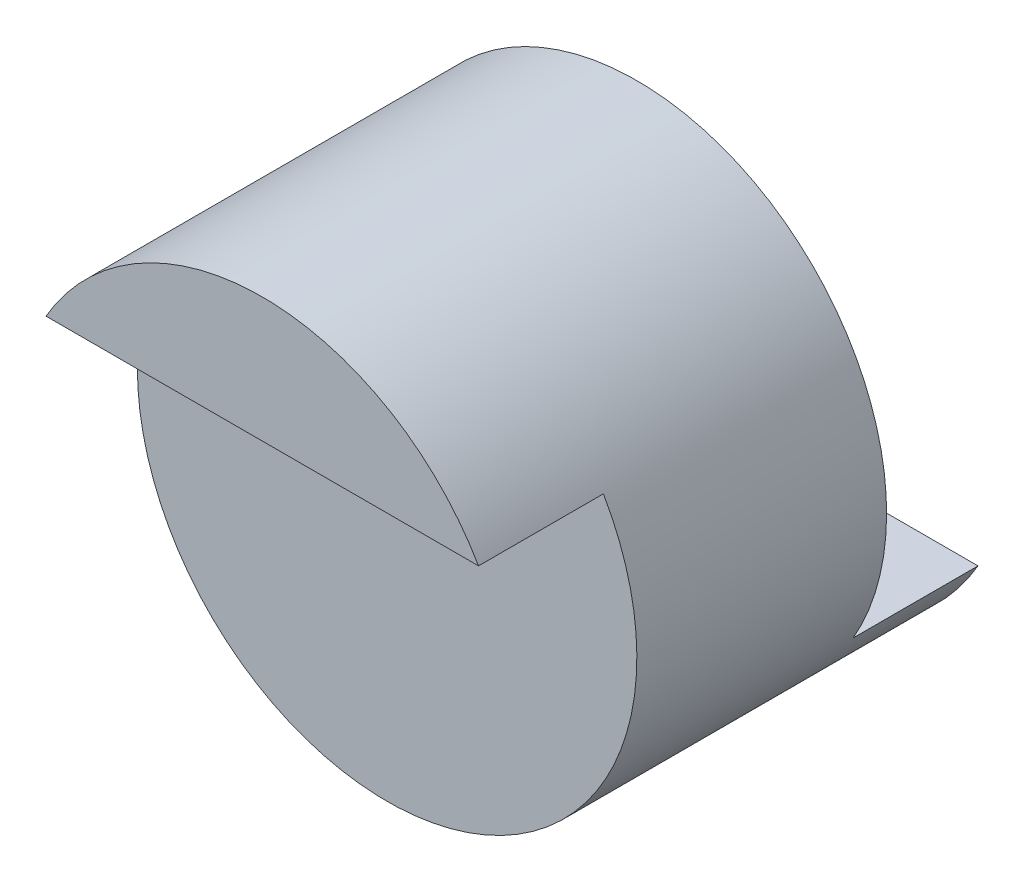
SolidWorks part; units mm, degrees
ref_plane "Front" through (0, 0, 0) normal (0, 0, 1) x (1, 0, 0)
ref_plane "Top" through (0, 0, 0) normal (0, 1, 0) x (1, 0, 0)
ref_plane "Right" through (0, 0, 0) normal (1, 0, 0) x (0, 0, -1)
sketch "Sketch1" plane through (0, 0, 0) normal (0, 0, 1) x (1, 0, 0)
  circle A0 centre (0, 0) radius 2
  dimension "D1" = 4
extrude "Boss-Extrude1" add sketch "Sketch1" along normal blind 2
sketch "Sketch2" plane through (0, 0, 2) normal (0, 0, 1) x (1, 0, 0)
  line L0 (-1.7321, 1) -> (1.7321, 1)
  circle A0 centre (0, 0) radius 2 construction
  arc A1 (-1.7321, 1) -> (1.7321, 1) centre (0, 0) cw
  dimension "D1" = 1
extrude "Boss-Extrude2" add sketch "Sketch2" along normal blind 1
sketch "Sketch3" plane through (0, 0, 0) normal (0, 0, -1) x (-1, 0, 0)
  line L0 (1.7321, -1) -> (-1.7321, -1)
  arc A0 (-1.7321, 1) -> (1.7321, 1) centre (0, 0) ccw construction
  arc A1 (1.7321, -1) -> (-1.7321, -1) centre (0, 0) cw
  dimension "D1" = 1
extrude "Boss-Extrude3" add sketch "Sketch3" along normal blind 1
